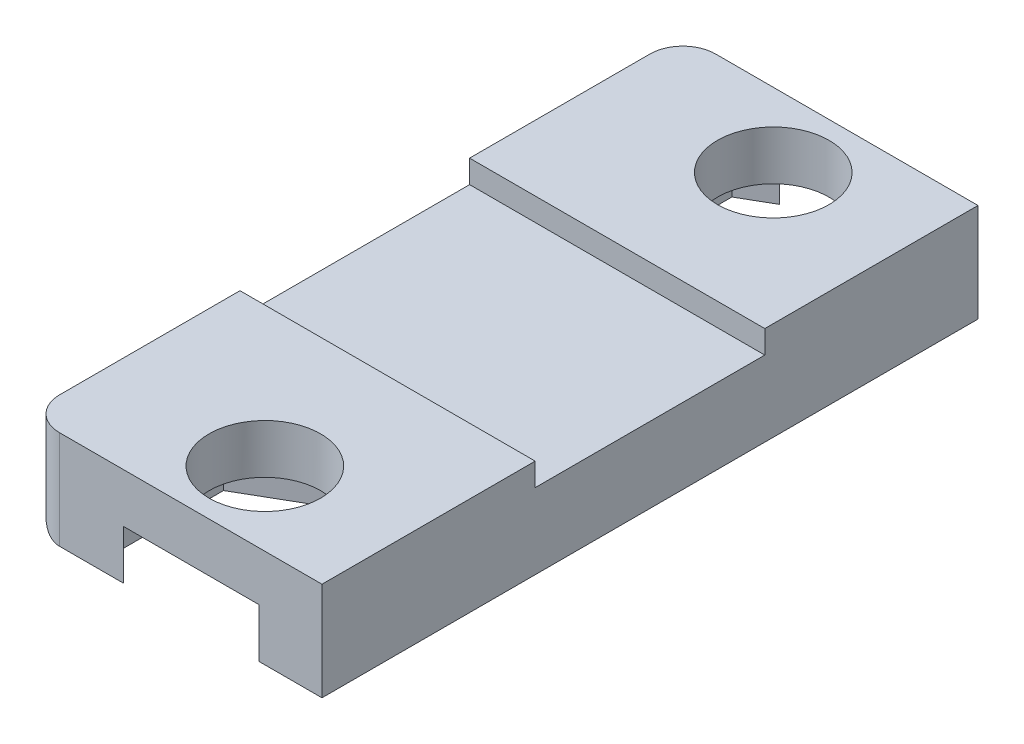
SolidWorks part; units mm, degrees
ref_plane "Alzado" through (0, 0, 0) normal (0, 0, 1) x (1, 0, 0)
ref_plane "Planta" through (0, 0, 0) normal (0, 1, 0) x (1, 0, 0)
ref_plane "Vista lateral" through (0, 0, 0) normal (1, 0, 0) x (0, 0, -1)
sketch "Croquis1" plane through (0, 0, 0) normal (0, 1, 0) x (1, 0, 0)
  line L1 (160.9544, -2) -> (169.9544, -2)
  line L2 (160.9544, -2) -> (160.9544, -22)
  line L3 (160.9544, -22) -> (169.9544, -22)
  line L4 (169.9544, -2) -> (169.9544, -22)
  circle A0 centre (165.9623, -4.25) radius 1.7
  circle A1 centre (165.9623, -19.75) radius 1.7
  dimension "D3" = 3.4
  dimension "D4" = 3.4
  dimension "D5" = 5.0079
  dimension "D6" = 2.25
  dimension "D1" = 20
  dimension "D2" = 9
  dimension "D7" = 15.5
extrude "Saliente-Extruir1" add sketch "Croquis1" against normal blind 3 separate body
sketch "Croquis2" plane through (0, -3, 0) normal (0, -1, 0) x (1, 0, 0)
  line L0 (160.9544, 2) -> (160.9544, 22) construction
  line L1 (168.9438, 21.4714) -> (165.9623, 23.1928)
  line L2 (165.9623, 23.1928) -> (162.9808, 21.4714)
  line L3 (162.9808, 21.4714) -> (162.9808, 18.0286)
  line L4 (162.9808, 18.0286) -> (165.9623, 16.3072)
  line L5 (165.9623, 16.3072) -> (168.9438, 18.0286)
  line L6 (168.9438, 18.0286) -> (168.9438, 21.4714)
  line L7 (160.9544, 12) -> (169.9544, 12) construction
  line L8 (169.9544, 22) -> (169.9544, 2) construction
  line L9 (168.9438, 5.9714) -> (168.9438, 2.5286)
  line L10 (165.9623, 7.6928) -> (168.9438, 5.9714)
  line L11 (162.9808, 5.9714) -> (165.9623, 7.6928)
  line L13 (162.9808, 2.5286) -> (162.9808, 5.9714)
  line L14 (165.9623, 0.8072) -> (162.9808, 2.5286)
  line L15 (168.9438, 2.5286) -> (165.9623, 0.8072)
  circle A0 centre (165.9623, 19.75) radius 2.9815 construction
  circle A1 centre (165.9623, 4.25) radius 2.9815 construction
extrude "Cortar-Extruir2" cut sketch "Croquis2" against normal blind 1.5
sketch "Croquis3" plane through (160.9544, 0, 0) normal (-1, 0, 0) x (0, 0, 1)
  line L0 (12, -3) -> (12, 0) construction
  line L1 (2, -3) -> (22, -3) construction
  line L2 (2, 0) -> (22, 0) construction
  line L4 (8.5, -1) -> (15.5, -1)
  line L5 (8.5, -1) -> (8.5, 0)
  line L6 (8.5, 0) -> (15.5, 0)
  line L7 (15.5, -1) -> (15.5, 0)
  line L8 (8.5, -1) -> (15.5, 0) construction
  line L9 (8.5, 0) -> (15.5, -1) construction
  point P6 (12, -0.5)
  dimension "D1" = 7
  dimension "D2" = 1
extrude "Cortar-Extruir3" cut sketch "Croquis3" against normal up to next
fillet "Redondeo1" radius 1 3 edges at (160.9544, -1.5, 2) (160.9544, -1.5, 22) (160.9544, -3, 12)
sketch "Croquis4" plane through (0, -1, 0) normal (0, 1, 0) x (1, 0, 0)
  line L1 (169.9544, -8.5) -> (160.9544, -8.5)
  line L2 (169.9544, -8.5) -> (169.9544, -15.5)
  line L3 (169.9544, -15.5) -> (160.9544, -15.5)
  line L4 (160.9544, -8.5) -> (160.9544, -15.5)
extrude "Saliente-Extruir2" add sketch "Croquis4" along normal blind 0.3
